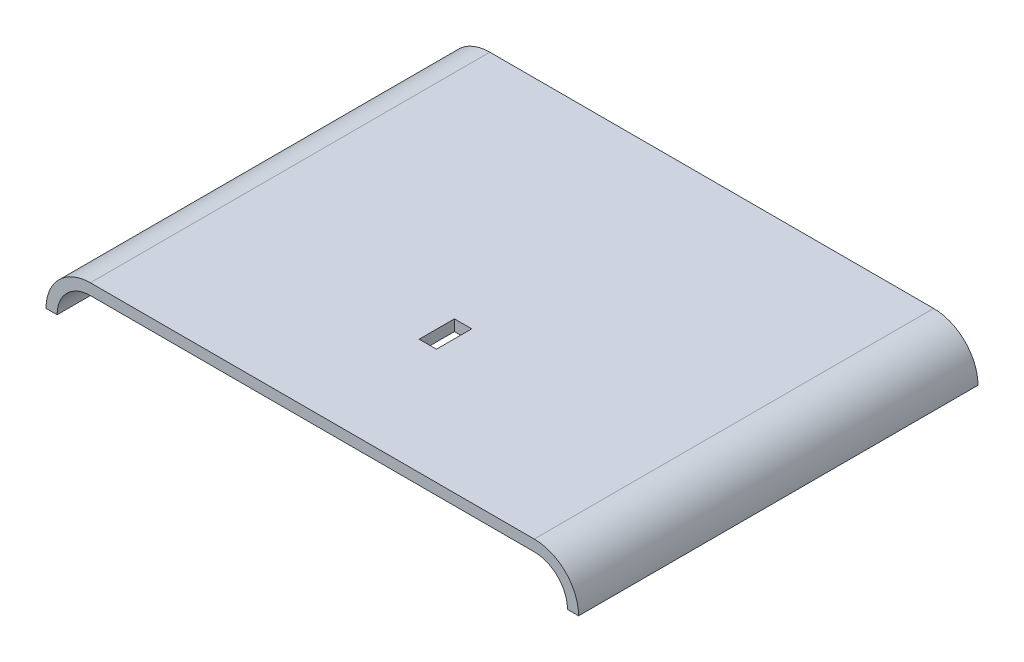
SolidWorks part; units mm, degrees
material "Expanded Polystyrene"
ref_plane "Front Plane" through (0, 0, 0) normal (0, 0, 1) x (1, 0, 0)
ref_plane "Top Plane" through (0, 0, 0) normal (0, 1, 0) x (1, 0, 0)
ref_plane "Right Plane" through (0, 0, 0) normal (1, 0, 0) x (0, 0, -1)
sketch "Sketch1" plane through (0, 0, 0) normal (0, 0, 1) x (1, 0, 0)
  line L0 (0, 18.4549) -> (0, 0) construction
  line L1 (0, 0) -> (254, 0)
  arc A0 (254, 0) -> (304.8, -50.8) centre (254, -50.8) cw
  dimension "D1" = 50.8
  dimension "D3" = 304.8
extrude "Extrude-Thin1" add sketch "Sketch1" along normal blind 457.2 thin
mirror "Mirror1" about plane through (0, -12.7, 457.2) normal (-1, 0, 0) of "Extrude-Thin1"
sketch "Sketch2" plane through (0, -50.8, 0) normal (0, -1, 0) x (1, 0, 0)
  line L0 (298.45, 0) -> (298.45, 457.2) construction
  line L1 (304.8, 0) -> (292.1, 0) construction
  line L2 (304.8, 457.2) -> (292.1, 457.2) construction
  line L3 (-298.45, 0) -> (-298.45, 457.2) construction
  line L4 (-304.8, 0) -> (-292.1, 0) construction
  line L5 (-304.8, 457.2) -> (-292.1, 457.2) construction
ref_plane "Plane1" through (0, 25.4, 0) normal (0, 1, 0) x (1, 0, 0)
sketch "Sketch4" plane through (0, 0, 0) normal (0, 1, 0) x (1, 0, 0)
  line L0 (254, -457.2) -> (-254, 0) construction
sketch "Sketch5" plane through (0, 0, 0) normal (0, 1, 0) x (1, 0, 0)
  line L0 (0, -304.8) -> (0, -457.2) construction
  line L1 (9.906, -284.607) -> (-9.906, -284.607)
  line L2 (9.906, -284.607) -> (9.906, -324.993)
  line L3 (9.906, -324.993) -> (-9.906, -324.993)
  line L4 (-9.906, -284.607) -> (-9.906, -324.993)
  line L5 (9.906, -284.607) -> (-9.906, -324.993) construction
  line L6 (9.906, -324.993) -> (-9.906, -284.607) construction
  line L7 (-254, -457.2) -> (254, -457.2) construction
  point P0 (0, -304.8)
  dimension "D1" = 19.812
  dimension "D2" = 40.386
  dimension "D3" = 152.4
extrude "Cut-Extrude1" cut sketch "Sketch5" against normal through all
